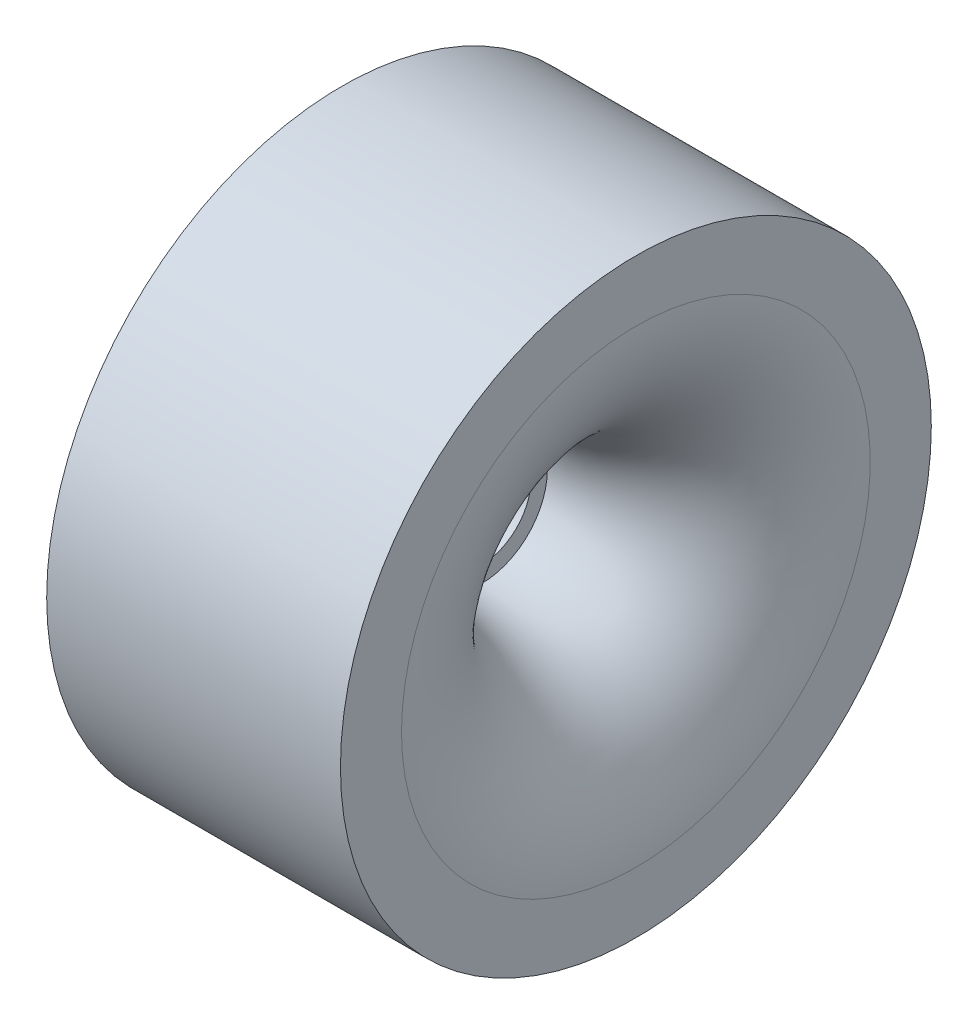
SolidWorks part; units mm, degrees
ref_plane "Front Plane" through (0, 0, 0) normal (0, 0, 1) x (1, 0, 0)
ref_plane "Top Plane" through (0, 0, 0) normal (0, 1, 0) x (1, 0, 0)
ref_plane "Right Plane" through (0, 0, 0) normal (1, 0, 0) x (0, 0, -1)
sketch "Sketch1" plane through (0, 0, 0) normal (0, 0, 1) x (1, 0, 0)
  line L0 (0, 0) -> (42.9034, 0) construction
  line L1 (0, 0) -> (0, 25) construction
  line L4 (10.6677, 30.0505) -> (15.6677, 30.0505)
  line L5 (15.6677, 30.0505) -> (15.6677, 23.8385)
  line L8 (0, 6.6569) -> (0, 10.5007)
  line L11 (13.2111, 23.8385) -> (-14.2111, 23.8385)
  line L12 (-14.2111, 23.8385) -> (-14.2111, 30.0505)
  line L13 (-14.2111, 30.0505) -> (-9.2111, 30.0505)
  line L16 (-9.2111, 30.0505) -> (10.6677, 30.0505)
  arc A0 (13.2111, 23.8385) -> (0, 10.5007) centre (1.186, 22.5376) cw
  arc A1 (15.6677, 23.8385) -> (0, 6.6569) centre (-1.2625, 23.5425) cw
  dimension "D3" = 6.2121
  dimension "D1" = 5
  dimension "D2" = 29.8789
revolve "Revolve1" add sketch "Sketch1" angle 360 about L0
sketch "Sketch2" plane through (0, 0, 0) normal (-1, 0, 0) x (0, 0, 1)
  circle A1 centre (0, 0) radius 10.5007
  circle A2 centre (0, 0) radius 10.5007
  circle A5 centre (0, 0) radius 5
  dimension "D2" = 10
  dimension "D1" = 0
extrude "Boss-Extrude2" add sketch "Sketch2" along normal blind 13.1828
